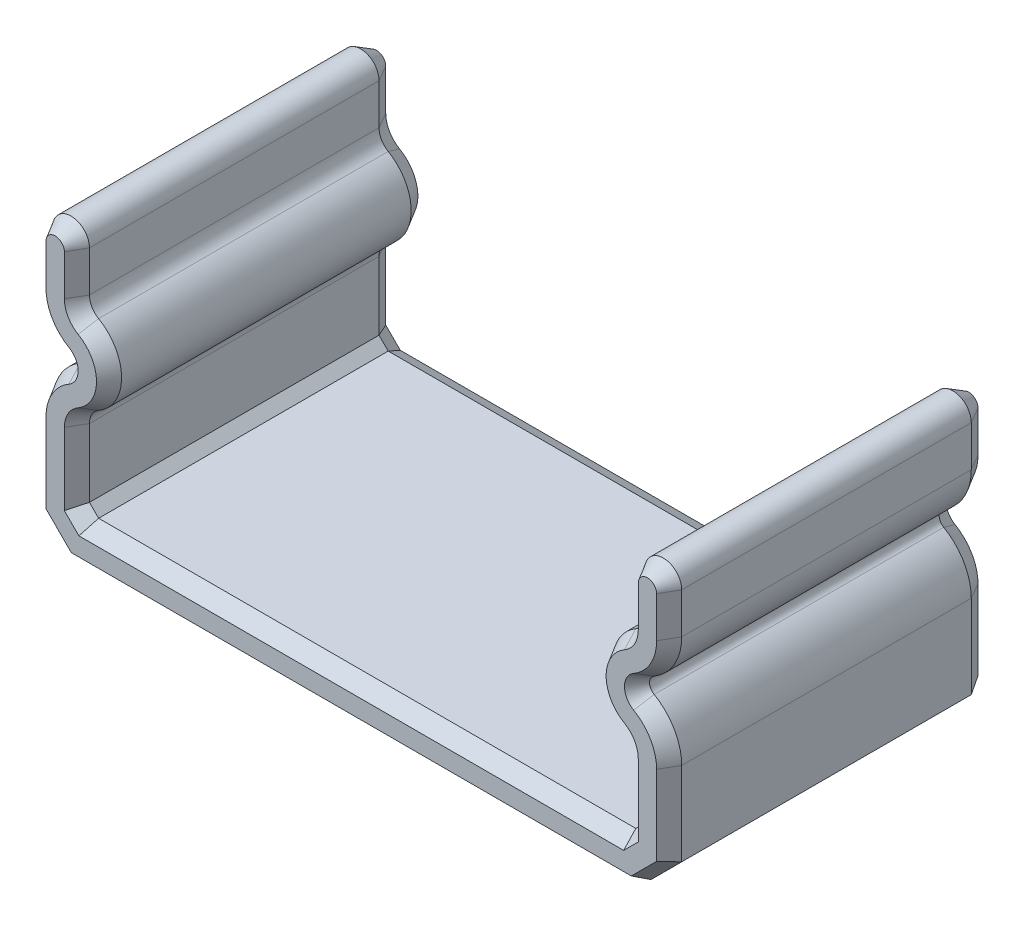
SolidWorks part; units mm, degrees
ref_plane "Front Plane" through (0, 0, 0) normal (0, 0, 1) x (1, 0, 0)
ref_plane "Top Plane" through (0, 0, 0) normal (0, 1, 0) x (1, 0, 0)
ref_plane "Right Plane" through (0, 0, 0) normal (1, 0, 0) x (0, 0, -1)
sketch "Sketch1" plane through (0, 0, 0) normal (0, 0, 1) x (1, 0, 0)
  line L0 (5.85, 0) -> (-5.85, 0)
  line L1 (-6.05, 0.2) -> (-6.05, 1.6876)
  line L2 (-5.85, 0) -> (-6.05, 0.2)
  line L3 (-6.05, 4.1124) -> (-6.05, 5)
  line L4 (0, 0) -> (0, 4.8196) construction
  line L5 (6.85, 4.1124) -> (6.85, 5)
  line L6 (6.85, -0.1314) -> (6.85, 1.6876)
  line L7 (6.05, 4.1124) -> (6.05, 5)
  line L8 (5.85, 0) -> (6.05, 0.2)
  line L9 (6.05, 0.2) -> (6.05, 1.6876)
  line L10 (6.1814, -0.8) -> (6.85, -0.1314)
  line L11 (6.1814, -0.8) -> (-6.1814, -0.8)
  line L12 (-6.1814, -0.8) -> (-6.85, -0.1314)
  line L13 (-6.85, -0.1314) -> (-6.85, 1.6876)
  line L14 (-6.85, 4.1124) -> (-6.85, 5)
  arc A0 (-5.85, 2.034) -> (-5.85, 3.766) centre (-6.35, 2.9) ccw
  arc A1 (-6.05, 1.6876) -> (-5.85, 2.034) centre (-5.65, 1.6876) cw
  arc A2 (-5.85, 3.766) -> (-6.05, 4.1124) centre (-5.65, 4.1124) cw
  arc A3 (5.85, 3.766) -> (6.05, 4.1124) centre (5.65, 4.1124) ccw
  arc A4 (6.05, 1.6876) -> (5.85, 2.034) centre (5.65, 1.6876) ccw
  arc A5 (5.85, 2.034) -> (5.85, 3.766) centre (6.35, 2.9) cw
  arc A6 (6.25, 3.0732) -> (6.85, 4.1124) centre (5.65, 4.1124) ccw
  arc A7 (6.25, 2.7268) -> (6.25, 3.0732) centre (6.35, 2.9) cw
  arc A8 (6.85, 1.6876) -> (6.25, 2.7268) centre (5.65, 1.6876) ccw
  arc A9 (-6.85, 1.6876) -> (-6.25, 2.7268) centre (-5.65, 1.6876) cw
  arc A10 (-6.25, 2.7268) -> (-6.25, 3.0732) centre (-6.35, 2.9) ccw
  arc A11 (-6.25, 3.0732) -> (-6.85, 4.1124) centre (-5.65, 4.1124) cw
  arc A12 (6.05, 5) -> (6.85, 5) centre (6.45, 5) cw
  arc A13 (-6.05, 5) -> (-6.85, 5) centre (-6.45, 5) ccw
  point P2 (-6.05, 0)
  point P4 (0, 0)
  point P27 (6.05, 0)
  dimension "D1" = 5
  dimension "D3" = 2
  dimension "D6" = 0.4
  dimension "D2" = 6.05
  dimension "D4" = 2.9
  dimension "D5" = 0.3
  dimension "D7" = 0.8
  dimension "D9" = 90
extrude "Boss-Extrude1" add sketch "Sketch1" along normal blind 7
chamfer "Chamfer1" distance 0.2 angle 60 56 edges at (-5.35, 2.9, 0) (-5.9964, 3.9124, 0) (-6.05, 4.5562, 0) (-6.45, 5.4, 0) (-6.85, 4.5562, 0) (-6.6892, 3.5124, 0) (-6.15, 2.9, 0) (-6.6892, 2.2876, 0) (-6.85, 0.7781, 0) (-6.5157, -0.4657, 0) (0, -0.8, 0) (6.5157, -0.4657, 0) (6.85, 0.7781, 0) (6.6892, 2.2876, 0) (6.15, 2.9, 0) (6.6892, 3.5124, 0) (6.85, 4.5562, 0) (6.45, 5.4, 0) (6.05, 4.5562, 0) (5.9964, 3.9124, 0) (5.35, 2.9, 0) (5.9964, 1.8876, 0) (6.05, 0.9438, 0) (5.95, 0.1, 0) (0, 0, 0) (-5.95, 0.1, 0) (-6.05, 0.9438, 0) (-5.9964, 1.8876, 0) (-6.05, 0.9438, 7) (-5.95, 0.1, 7) (0, 0, 7) (5.95, 0.1, 7) (6.05, 0.9438, 7) (5.9964, 1.8876, 7) (5.35, 2.9, 7) (5.9964, 3.9124, 7) (6.05, 4.5562, 7) (6.45, 5.4, 7) (6.85, 4.5562, 7) (6.6892, 3.5124, 7) (6.15, 2.9, 7) (6.6892, 2.2876, 7) (6.85, 0.7781, 7) (6.5157, -0.4657, 7) (0, -0.8, 7) (-6.5157, -0.4657, 7) (-6.85, 0.7781, 7) (-6.6892, 2.2876, 7) (-6.15, 2.9, 7) (-6.6892, 3.5124, 7) (-6.85, 4.5562, 7) (-6.45, 5.4, 7) (-6.05, 4.5562, 7) (-5.9964, 3.9124, 7) (-5.35, 2.9, 7) (-5.9964, 1.8876, 7)
